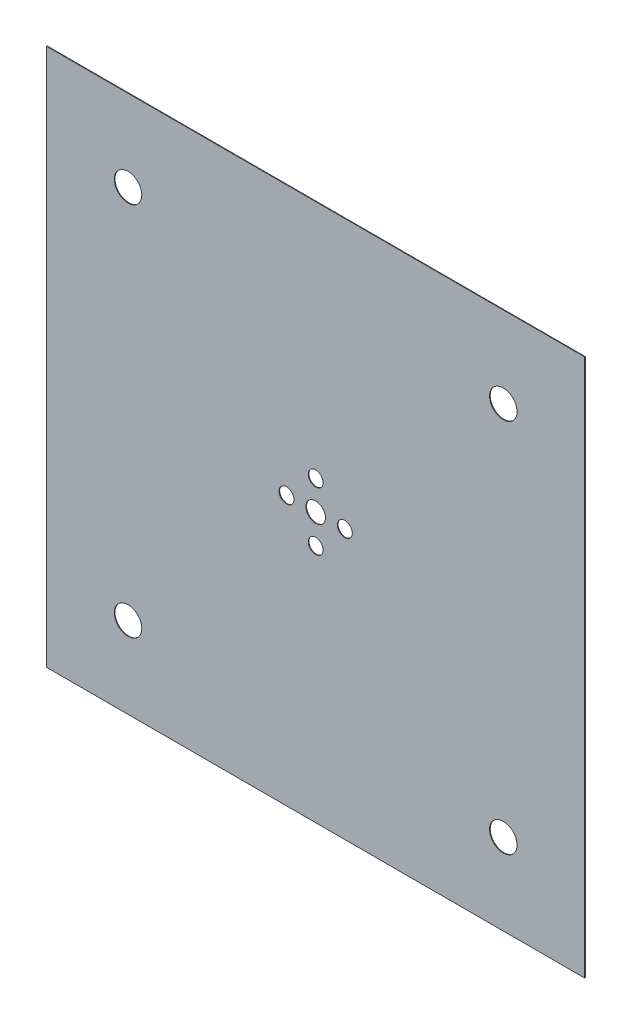
SolidWorks part; units mm, degrees
ref_plane "Front" through (0, 0, 0) normal (0, 0, 1) x (1, 0, 0)
ref_plane "Top" through (0, 0, 0) normal (0, 1, 0) x (1, 0, 0)
ref_plane "Right" through (0, 0, 0) normal (1, 0, 0) x (0, 0, -1)
sketch "Sketch1" plane through (0, 0, 0) normal (0, 0, 1) x (1, 0, 0)
  line L0 (-1290, 0) -> (1290, 0) construction
  line L1 (-1290, 1290) -> (1290, 1290)
  line L2 (-1290, 1290) -> (-1290, -1290)
  line L3 (-1290, -1290) -> (1290, -1290)
  line L4 (1290, 1290) -> (1290, -1290)
  line L5 (-1290, 1290) -> (1290, -1290) construction
  line L6 (-1290, -1290) -> (1290, 1290) construction
  line L7 (0, 1290) -> (0, -1290) construction
  circle A0 centre (0, 0) radius 46.75
  circle A1 centre (0, 140) radius 35.6375
  circle A2 centre (-900, 900) radius 65.8
  circle A3 centre (900, 900) radius 65.8
  circle A4 centre (140, 0) radius 35.6375
  circle A5 centre (900, -900) radius 65.8
  circle A6 centre (-900, -900) radius 65.8
  circle A7 centre (0, -140) radius 35.6375
  circle A8 centre (-140, 0) radius 35.6375
  point P0 (0, 0)
  dimension "D3" = 93.5
  dimension "D4" = 71.275
  dimension "D6" = 131.6
  dimension "D1" = 2580
  dimension "D2" = 2580
  dimension "D5" = 140
  dimension "D7" = 900
extrude "Boss-Extrude1" add sketch "Sketch1" along normal blind 3
